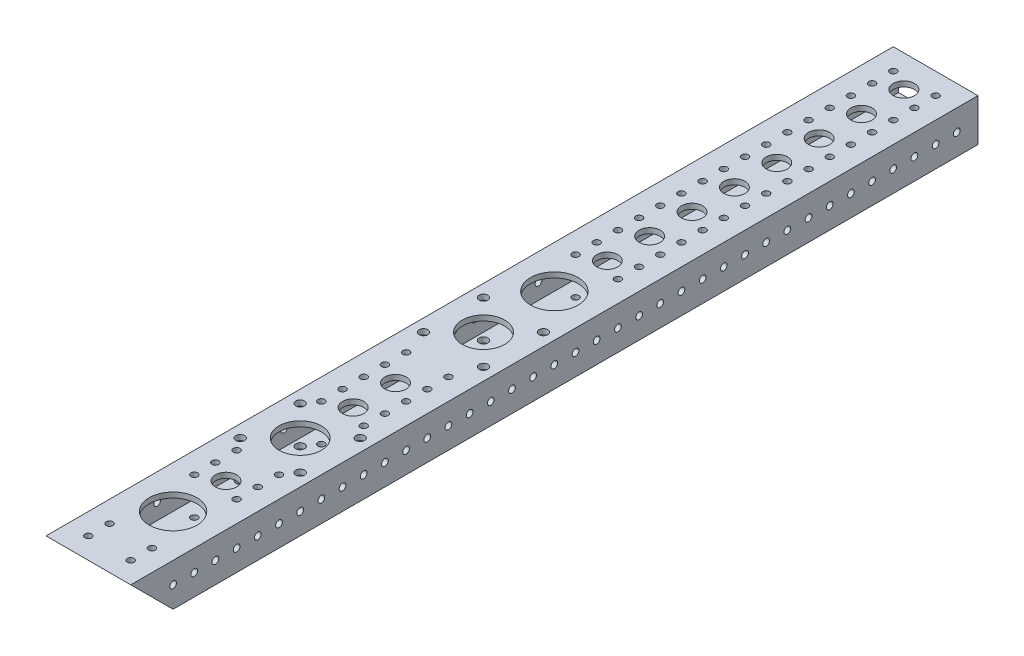
SolidWorks part; units mm, degrees
other "Markup1"
sketch "Sketch9" plane through (0, 25.4, 508) normal (-0.1403, 0.9439, 0.2991) x (-0.0228, 0.2989, -0.954)
material "6061 Alloy"
ref_plane "Front Plane" through (0, 0, 0) normal (0, 0, 1) x (1, 0, 0)
ref_plane "Top Plane" through (0, 0, 0) normal (0, 1, 0) x (1, 0, 0)
ref_plane "Right Plane" through (0, 0, 0) normal (1, 0, 0) x (0, 0, -1)
sketch "Sketch1" plane through (0, 0, 0) normal (0, 0, 1) x (1, 0, 0)
  line L0 (3.175, 22.225) -> (47.625, 22.225)
  line L1 (0, 0) -> (50.8, 0)
  line L2 (0, 0) -> (0, 25.4)
  line L3 (0, 25.4) -> (50.8, 25.4)
  line L4 (50.8, 0) -> (50.8, 25.4)
  line L5 (47.625, 3.175) -> (47.625, 22.225)
  line L6 (3.175, 3.175) -> (47.625, 3.175)
  line L7 (3.175, 3.175) -> (3.175, 22.225)
  dimension "D1" = 50.8
  dimension "D2" = 25.4
  dimension "D3" = 3.175
extrude "Boss-Extrude1" add sketch "Sketch1" along normal blind 508
sketch "Sketch2" plane through (0, 25.4, 0) normal (0, 1, 0) x (1, 0, 0)
  line L2 (50.8, 0) -> (0, 0) construction
  line L3 (12.7, -495.3) -> (12.7, -482.6) construction
  line L4 (0, -508) -> (12.7, -508) construction
  line L5 (0, -508) -> (0, -495.3) construction
  line L6 (0, -495.3) -> (12.7, -495.3) construction
  line L7 (12.7, -508) -> (12.7, -495.3) construction
  line L8 (0, -508) -> (0, 0) construction
  circle A0 centre (12.7, -495.3) radius 2.0193
  circle A2 centre (38.1, -495.3) radius 2.0193
  circle A11 centre (12.7, -431.8) radius 2.0193
  circle A12 centre (38.1, -431.8) radius 2.0193
  circle A13 centre (12.7, -419.1) radius 2.0193
  circle A14 centre (38.1, -419.1) radius 2.0193
  circle A15 centre (12.7, -406.4) radius 2.0193
  circle A16 centre (38.1, -406.4) radius 2.0193
  circle A23 centre (12.7, -355.6) radius 2.0193
  circle A24 centre (38.1, -355.6) radius 2.0193
  circle A25 centre (12.7, -342.9) radius 2.0193
  circle A26 centre (38.1, -342.9) radius 2.0193
  circle A27 centre (12.7, -330.2) radius 2.0193
  circle A28 centre (38.1, -330.2) radius 2.0193
  circle A29 centre (12.7, -317.5) radius 2.0193
  circle A30 centre (38.1, -317.5) radius 2.0193
  circle A31 centre (12.7, -304.8) radius 2.0193
  circle A32 centre (38.1, -304.8) radius 2.0193
  circle A47 centre (12.7, -203.2) radius 2.0193
  circle A48 centre (38.1, -203.2) radius 2.0193
  circle A49 centre (12.7, -190.5) radius 2.0193
  circle A50 centre (38.1, -190.5) radius 2.0193
  circle A51 centre (12.7, -177.8) radius 2.0193
  circle A52 centre (38.1, -177.8) radius 2.0193
  circle A53 centre (12.7, -165.1) radius 2.0193
  circle A54 centre (38.1, -165.1) radius 2.0193
  circle A55 centre (12.7, -152.4) radius 2.0193
  circle A56 centre (38.1, -152.4) radius 2.0193
  circle A57 centre (12.7, -139.7) radius 2.0193
  circle A58 centre (38.1, -139.7) radius 2.0193
  circle A59 centre (12.7, -127) radius 2.0193
  circle A60 centre (38.1, -127) radius 2.0193
  circle A61 centre (12.7, -114.3) radius 2.0193
  circle A62 centre (38.1, -114.3) radius 2.0193
  circle A63 centre (12.7, -101.6) radius 2.0193
  circle A64 centre (38.1, -101.6) radius 2.0193
  circle A65 centre (12.7, -88.9) radius 2.0193
  circle A66 centre (38.1, -88.9) radius 2.0193
  circle A67 centre (12.7, -76.2) radius 2.0193
  circle A68 centre (38.1, -76.2) radius 2.0193
  circle A69 centre (12.7, -63.5) radius 2.0193
  circle A70 centre (38.1, -63.5) radius 2.0193
  circle A71 centre (12.7, -50.8) radius 2.0193
  circle A72 centre (38.1, -50.8) radius 2.0193
  circle A73 centre (12.7, -38.1) radius 2.0193
  circle A74 centre (38.1, -38.1) radius 2.0193
  circle A75 centre (12.7, -25.4) radius 2.0193
  circle A76 centre (38.1, -25.4) radius 2.0193
  circle A77 centre (12.7, -12.7) radius 2.0193
  circle A78 centre (38.1, -12.7) radius 2.0193
  circle A98 centre (25.4, -19.05) radius 6.35
  circle A99 centre (12.7, -381) radius 2.0193 [skipped]
  circle A100 centre (38.1, -381) radius 2.0193 [skipped]
  circle A101 centre (25.4, -44.45) radius 6.35
  circle A102 centre (12.7, -292.1) radius 2.0193 [skipped]
  circle A103 centre (38.1, -292.1) radius 2.0193 [skipped]
  circle A104 centre (25.4, -69.85) radius 6.35
  circle A105 centre (12.7, -266.7) radius 2.0193 [skipped]
  circle A106 centre (38.1, -266.7) radius 2.0193 [skipped]
  circle A107 centre (12.7, -279.4) radius 2.0193 [skipped]
  circle A108 centre (38.1, -279.4) radius 2.0193 [skipped]
  circle A109 centre (25.4, -95.25) radius 6.35
  circle A110 centre (12.7, -254) radius 2.0193 [skipped]
  circle A111 centre (38.1, -254) radius 2.0193 [skipped]
  circle A112 centre (12.7, -228.6) radius 2.0193 [skipped]
  circle A113 centre (38.1, -228.6) radius 2.0193 [skipped]
  circle A114 centre (25.4, -120.65) radius 6.35
  circle A115 centre (12.7, -393.7) radius 2.0193 [skipped]
  circle A116 centre (38.1, -393.7) radius 2.0193 [skipped]
  circle A117 centre (12.7, -368.3) radius 2.0193 [skipped]
  circle A118 centre (38.1, -368.3) radius 2.0193 [skipped]
  circle A119 centre (12.7, -241.3) radius 2.0193 [skipped]
  circle A120 centre (38.1, -241.3) radius 2.0193 [skipped]
  circle A121 centre (38.1, -215.9) radius 2.0193 [skipped]
  circle A122 centre (12.7, -215.9) radius 2.0193 [skipped]
  circle A123 centre (38.1, -482.6) radius 2.0193 [skipped]
  circle A124 centre (12.7, -482.6) radius 2.0193 [skipped]
  circle A125 centre (25.4, -146.05) radius 6.35
  circle A126 centre (25.4, -171.45) radius 6.35
  circle A127 centre (25.4, -196.85) radius 6.35
  circle A132 centre (25.4, -323.85) radius 6.35
  circle A133 centre (25.4, -349.25) radius 6.35
  circle A136 centre (25.4, -425.45) radius 6.35
  circle A139 centre (25.4, -222.25) radius 6.35 [skipped]
  circle A140 centre (25.4, -247.65) radius 6.35 [skipped]
  circle A141 centre (25.4, -273.05) radius 6.35 [skipped]
  circle A142 centre (25.4, -298.45) radius 6.35 [skipped]
  circle A143 centre (25.4, -476.25) radius 6.35 [skipped]
  circle A144 centre (25.4, -374.65) radius 6.35 [skipped]
  circle A145 centre (25.4, -400.05) radius 6.35 [skipped]
  circle A146 centre (12.7, -457.2) radius 2.0193 [skipped]
  circle A147 centre (38.1, -457.2) radius 2.0193 [skipped]
  circle A148 centre (25.4, -450.85) radius 6.35 [skipped]
  circle A149 centre (12.7, -469.9) radius 2.0193 [skipped]
  circle A150 centre (38.1, -469.9) radius 2.0193 [skipped]
  circle A151 centre (38.1, -444.5) radius 2.0193 [skipped]
  circle A152 centre (12.7, -444.5) radius 2.0193 [skipped]
  dimension "D3" = 4.0386
  dimension "D4" = 12.7
  dimension "D1" = 12.7
  dimension "D2" = 12.7
  dimension "D5" = 19.05
  dimension "D7" = 12.7
  dimension "D9" = 19
  dimension "D8" = 25.4
  dimension "D6" = 39
extrude "Cut-Extrude1" cut sketch "Sketch2" against normal blind 63.5
sketch "Sketch3" plane through (50.8, 0, 0) normal (1, 0, 0) x (0, 0, -1)
  line L0 (-508, 12.7) -> (0, 12.7) construction
  line L1 (-508, 0) -> (-508, 25.4) construction
  line L2 (0, 0) -> (0, 25.4) construction
  circle A1 centre (-482.6, 12.7) radius 2.0193
  circle A2 centre (-469.9, 12.7) radius 2.0193
  circle A3 centre (-457.2, 12.7) radius 2.0193
  circle A4 centre (-444.5, 12.7) radius 2.0193
  circle A5 centre (-431.8, 12.7) radius 2.0193
  circle A6 centre (-419.1, 12.7) radius 2.0193
  circle A7 centre (-406.4, 12.7) radius 2.0193
  circle A8 centre (-393.7, 12.7) radius 2.0193
  circle A9 centre (-381, 12.7) radius 2.0193
  circle A10 centre (-368.3, 12.7) radius 2.0193
  circle A11 centre (-355.6, 12.7) radius 2.0193
  circle A12 centre (-342.9, 12.7) radius 2.0193
  circle A13 centre (-330.2, 12.7) radius 2.0193
  circle A14 centre (-317.5, 12.7) radius 2.0193
  circle A15 centre (-304.8, 12.7) radius 2.0193
  circle A16 centre (-292.1, 12.7) radius 2.0193
  circle A17 centre (-279.4, 12.7) radius 2.0193
  circle A18 centre (-266.7, 12.7) radius 2.0193
  circle A19 centre (-254, 12.7) radius 2.0193
  circle A20 centre (-241.3, 12.7) radius 2.0193
  circle A21 centre (-228.6, 12.7) radius 2.0193
  circle A22 centre (-215.9, 12.7) radius 2.0193
  circle A23 centre (-203.2, 12.7) radius 2.0193
  circle A24 centre (-190.5, 12.7) radius 2.0193
  circle A25 centre (-177.8, 12.7) radius 2.0193
  circle A26 centre (-165.1, 12.7) radius 2.0193
  circle A27 centre (-152.4, 12.7) radius 2.0193
  circle A28 centre (-139.7, 12.7) radius 2.0193
  circle A29 centre (-127, 12.7) radius 2.0193
  circle A30 centre (-114.3, 12.7) radius 2.0193
  circle A31 centre (-101.6, 12.7) radius 2.0193
  circle A32 centre (-88.9, 12.7) radius 2.0193
  circle A33 centre (-76.2, 12.7) radius 2.0193
  circle A34 centre (-63.5, 12.7) radius 2.0193
  circle A35 centre (-50.8, 12.7) radius 2.0193
  circle A36 centre (-38.1, 12.7) radius 2.0193
  circle A37 centre (-25.4, 12.7) radius 2.0193
  circle A38 centre (-12.7, 12.7) radius 2.0193
extrude "Cut-Extrude2" cut sketch "Sketch3" against normal blind 63.5
hole_wizard "F (1.125) Diameter Hole1" positions "Sketch5" profile "Sketch6" hole size "F" standard "ANSI Inch" end condition through all
sketch "Sketch5" plane through (0, 25.4, 0) normal (0, 1, 0) x (1, 0, 0)
  line L0 (0, -508) -> (0, 0) construction
  line L1 (50.8, -508) -> (0, -508) construction
  point P0 (25.4, -228.6)
  point P7 (25.4, -457.2)
  dimension "D1" = 25.4
  dimension "D2" = 279.4
  dimension "D3" = 228.6
sketch "Sketch6" plane through (25.4, 25.4, 228.6) normal (1, 0, 0) x (0, 0, 1)
  line L0 (0, 0) -> (0, 25.4)
  line L1 (0, 25.4) -> (14.2875, 25.4)
  line L2 (14.2875, 25.4) -> (14.2875, 0)
  line L5 (14.2875, 0) -> (0, 0)
  line L11 (0, -6.35) -> (0, 107.95) construction
  dimension "Thru Hole Dia." = 28.575
  dimension "Thru Hole Depth" = 25.4
sketch "Sketch7" plane through (0, 25.4, 0) normal (0, 1, 0) x (1, 0, 0)
  line L0 (25.4, -381) -> (43.3605, -363.0395) construction
  line L1 (25.4, -381) -> (30.1609, -381) construction
  line L2 (50.8, -508) -> (0, -508) construction
  line L3 (25.4, -271.0942) -> (43.3605, -253.1337) construction
  line L4 (25.4, -271.0942) -> (30.1609, -271.0942) construction
  line L5 (0, -508) -> (0, 0) construction
  circle A0 centre (25.4, -381) radius 12.7
  circle A1 centre (43.3605, -363.0395) radius 2.6289
  circle A2 centre (43.3605, -398.9605) radius 2.6289
  circle A3 centre (7.4395, -398.9605) radius 2.6289
  circle A4 centre (7.4395, -363.0395) radius 2.6289
  circle A5 centre (25.4, -381) radius 25.4 construction
  circle A6 centre (25.4, -271.0942) radius 12.7
  circle A7 centre (43.3605, -253.1337) radius 2.6289
  circle A8 centre (43.3605, -289.0547) radius 2.6289
  circle A9 centre (7.4395, -289.0547) radius 2.6289
  circle A10 centre (7.4395, -253.1337) radius 2.6289
  circle A11 centre (25.4, -271.0942) radius 25.4 construction
  circle A12 centre (25.4, -228.6) radius 14.2875 construction
  point P15 (25.4, -381)
  point P26 (-11.5934, -281.296)
  dimension "D1" = 25.4
  dimension "D3" = 5.2578
  dimension "D6" = 127
  dimension "D7" = 25.4
  dimension "D9" = 5.2578
  dimension "D2" = 25.4
  dimension "D4" = 45
  dimension "D8" = 25.4
  dimension "D10" = 45
  dimension "D11" = 25.4
  dimension "D12" = 42.4942
  dimension "D5" = 4
extrude "Cut-Extrude3" cut sketch "Sketch7" against normal through all
sketch "Sketch8" plane through (0, 0, 0) normal (-1, 0, 0) x (0, 0, 1)
  line L0 (508, 25.4) -> (482.6, 0)
  line L1 (508, 0) -> (0, 0) construction
  line L2 (482.6, 0) -> (508, 0)
  line L3 (508, 0) -> (508, 25.4)
  dimension "D1" = 25.4
extrude "Cut-Extrude4" cut sketch "Sketch8" against normal through all
sketch "Sketch10" plane through (0, 25.4, 0) normal (0, 1, 0) x (1, 0, 0)
  line L2 (50.8, -508) -> (50.8, 0) construction
  line L3 (0, -508) -> (0, 0) construction
  line L4 (50.8, -508) -> (0, -508) construction
  circle A1 centre (38.1, -482.6) radius 2.0193
  circle A2 centre (12.7, -482.6) radius 2.0193
  circle A3 centre (12.7, -495.3) radius 2.0193 construction
  dimension "D1" = 12.7
  dimension "D4" = 12.7
  dimension "D5" = 4.0386
  dimension "D8" = 4.0386
  dimension "D2" = 25.4
  dimension "D6" = 12.7
extrude "Cut-Extrude5" cut sketch "Sketch10" against normal up to next
sketch "Sketch11" [suppressed] plane through (0, 0, 0) normal (0, -1, 0) x (1, 0, 0)
  line L0 (0, 482.6) -> (0, 0) construction
  line L1 (44.45, 292.8647) -> (6.35, 292.8647)
  line L2 (44.45, 292.8647) -> (44.45, 203.9647)
  line L3 (44.45, 203.9647) -> (6.35, 203.9647)
  line L4 (6.35, 292.8647) -> (6.35, 203.9647)
  line L5 (50.8, 482.6) -> (50.8, 0) construction
  circle A0 centre (7.4395, 289.0547) radius 2.6289 construction
  dimension "D1" = 6.35
  dimension "D2" = 6.35
  dimension "D3" = 88.9
  dimension "D4" = 3.81
extrude "Cut-Extrude6" [suppressed] cut sketch "Sketch11" against normal blind 3.175
